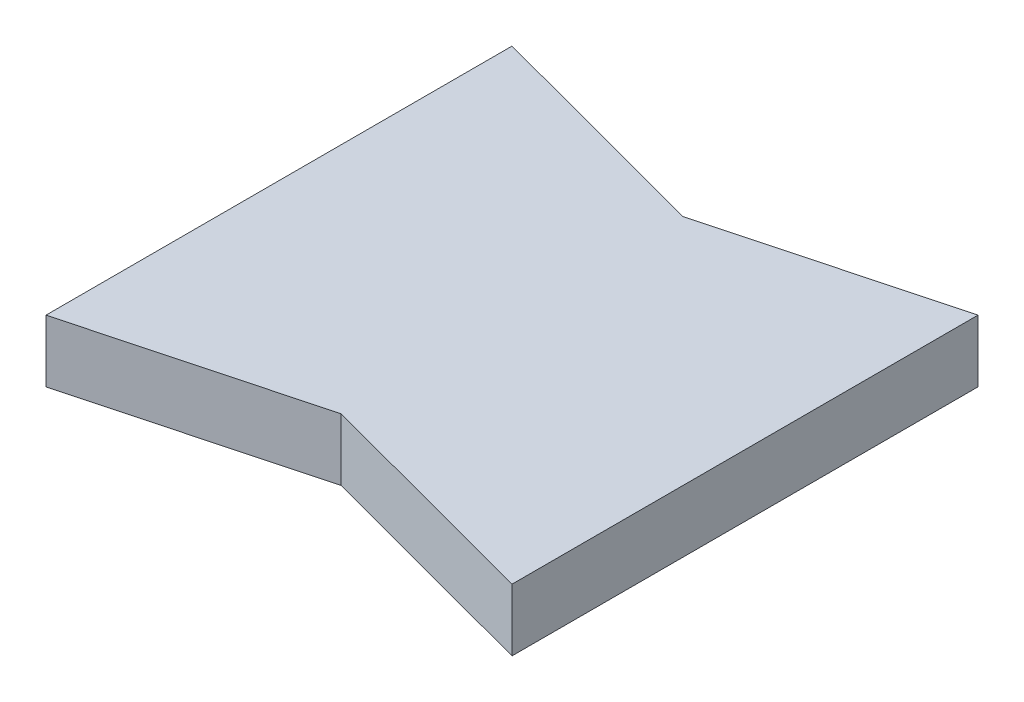
SolidWorks part; units mm, degrees
ref_plane "Front Plane" through (0, 0, 0) normal (0, 0, 1) x (1, 0, 0)
ref_plane "Top Plane" through (0, 0, 0) normal (0, 1, 0) x (1, 0, 0)
ref_plane "Right Plane" through (0, 0, 0) normal (1, 0, 0) x (0, 0, -1)
sketch "Sketch1" plane through (0, 0, 0) normal (0, 1, 0) x (1, 0, 0)
  line L0 (-33.9927, 12.1245) -> (-18.9927, 8.1245)
  line L5 (-18.9927, 8.1245) -> (-3.9927, 12.1245)
  line L6 (-33.9927, -17.8755) -> (-18.9927, -13.8755)
  line L7 (-18.9927, -13.8755) -> (-3.9927, -17.8755)
  line L8 (-33.9927, 12.1245) -> (-33.9927, -17.8755)
  line L9 (-3.9927, 12.1245) -> (-3.9927, -17.8755)
  dimension "D1" = 30
  dimension "D2" = 30
  dimension "D3" = 4
  dimension "D4" = 4
  dimension "D5" = 30
  dimension "D6" = 15
  dimension "D7" = 15
extrude "Boss-Extrude2" add sketch "Sketch1" along normal blind 4
